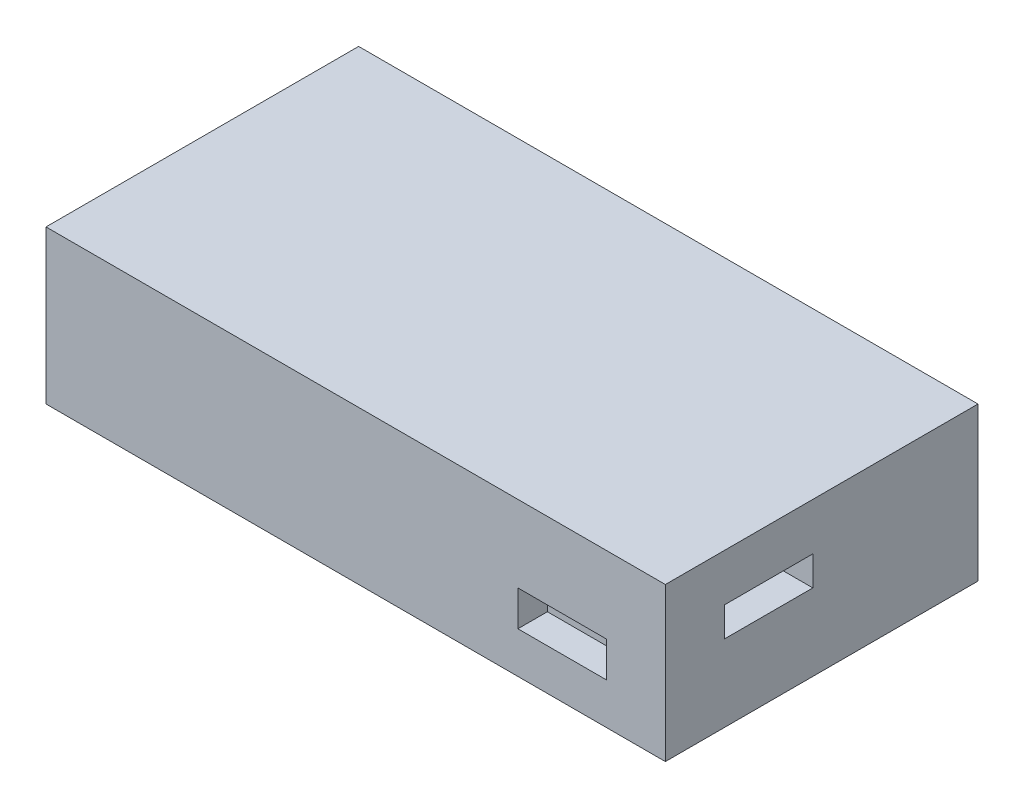
SolidWorks part; units mm, degrees
ref_plane "前视基准面" through (0, 0, 0) normal (0, 0, 1) x (1, 0, 0)
ref_plane "上视基准面" through (0, 0, 0) normal (0, 1, 0) x (1, 0, 0)
ref_plane "右视基准面" through (0, 0, 0) normal (1, 0, 0) x (0, 0, -1)
sketch "Sketch2" plane through (0, 0, 0) normal (0, 1, 0) x (1, 0, 0)
  line L1 (0, 0) -> (105, 0)
  line L2 (0, 0) -> (0, 53)
  line L3 (0, 53) -> (105, 53)
  line L4 (105, 0) -> (105, 53)
  dimension "D1" = 105
  dimension "D2" = 53
extrude "Boss-Extrude1" add sketch "Sketch2" along normal blind 26
sketch "Sketch3" plane through (0, 0, 0) normal (0, 0, 1) x (1, 0, 0)
  line L0 (95, 7) -> (80, 7)
  line L1 (80, 7) -> (80, 13)
  line L2 (80, 13) -> (95, 13)
  line L3 (95, 13) -> (95, 7)
  line L4 (105, 26) -> (105, 0) construction
  line L5 (0, 26) -> (105, 26) construction
  dimension "D1" = 10
  dimension "D2" = 25
  dimension "D3" = 13
  dimension "D4" = 6
extrude "Cut-Extrude1" cut sketch "Sketch3" against normal blind 5
sketch "Sketch4" plane through (105, 0, 0) normal (1, 0, 0) x (0, 0, -1)
  line L0 (10, 18) -> (10, 13)
  line L1 (10, 13) -> (25, 13)
  line L2 (25, 13) -> (25, 18)
  line L3 (25, 18) -> (10, 18)
  line L4 (0, 26) -> (0, 0) construction
  line L5 (0, 26) -> (53, 26) construction
  dimension "D1" = 15
  dimension "D2" = 5
  dimension "D3" = 10
  dimension "D4" = 8
extrude "Cut-Extrude2" cut sketch "Sketch4" against normal blind 10
